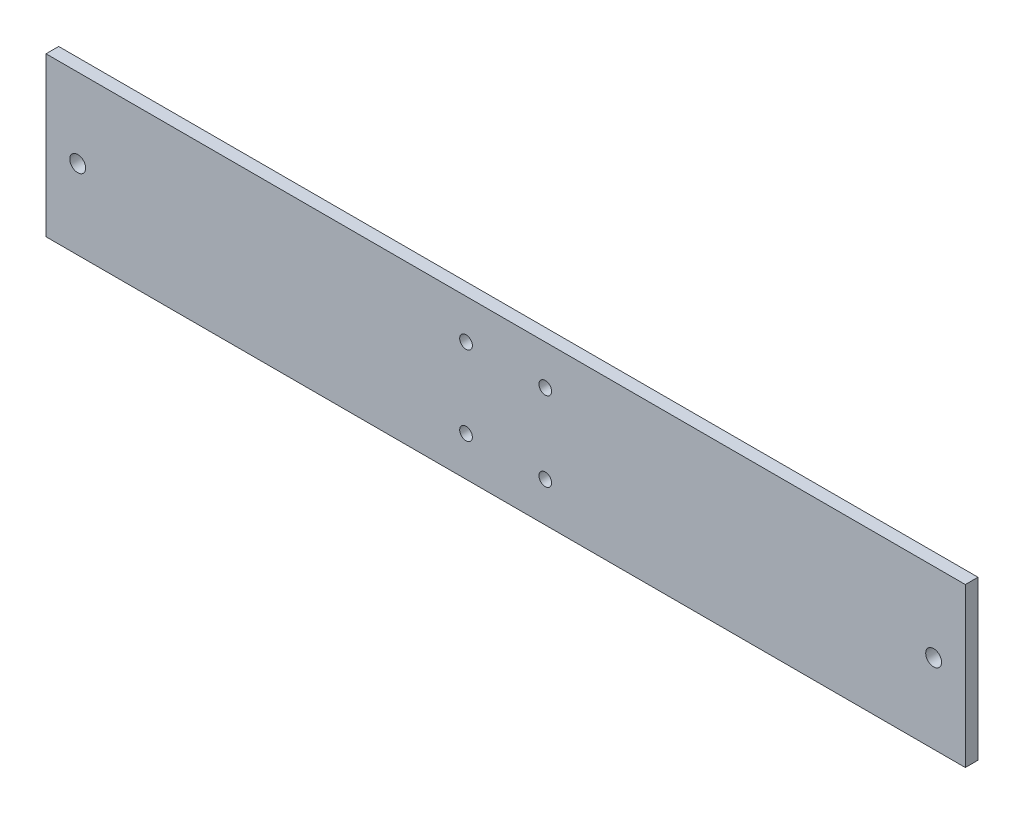
SolidWorks part; units mm, degrees
ref_plane "Front Plane" through (0, 0, 0) normal (0, 0, 1) x (1, 0, 0)
ref_plane "Top Plane" through (0, 0, 0) normal (0, 1, 0) x (1, 0, 0)
ref_plane "Right Plane" through (0, 0, 0) normal (1, 0, 0) x (0, 0, -1)
sketch "Sketch1" plane through (0, 0, 0) normal (0, 0, 1) x (1, 0, 0)
  line L0 (0, -25) -> (0, 25) construction
  line L1 (145, -25) -> (-145, -25)
  line L2 (145, -25) -> (145, 25)
  line L3 (145, 25) -> (-145, 25)
  line L4 (-145, -25) -> (-145, 25)
  line L5 (145, -25) -> (-145, 25) construction
  line L6 (145, 25) -> (-145, -25) construction
  line L7 (-145, 0) -> (145, 0) construction
  circle A0 centre (-12.5, 12.5) radius 2
  circle A1 centre (12.5, 12.5) radius 2
  circle A2 centre (12.5, -12.5) radius 2
  circle A3 centre (-12.5, -12.5) radius 2
  point P0 (0, 0)
  point P21 (0, 0)
  dimension "D3" = 4
  dimension "D4" = 25
  dimension "D5" = 25
  dimension "D6" = 4
  dimension "D1" = 290
  dimension "D2" = 50
extrude "Boss-Extrude1" add sketch "Sketch1" along normal blind 4
sketch "Sketch2" plane through (0, 0, 4) normal (0, 0, 1) x (1, 0, 0)
  line L0 (-145, 25) -> (-145, -25) construction
  line L1 (145, -25) -> (145, 25) construction
  circle A0 centre (-135, 0) radius 2.5
  circle A1 centre (135, 0) radius 2.5
  point P4 (0, 0)
  dimension "D1" = 5
  dimension "5" = 5
  dimension "D2" = 10
  dimension "D3" = 10
extrude "Cut-Extrude1" cut sketch "Sketch2" against normal blind 4
